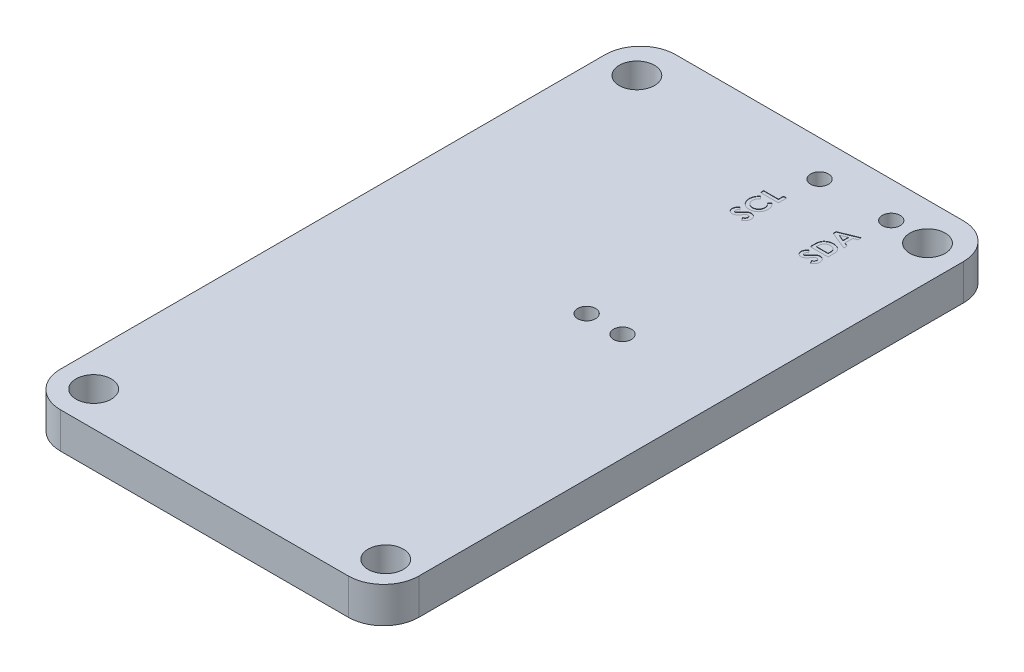
SolidWorks part; units mm, degrees
ref_plane "Front Plane" through (0, 0, 0) normal (0, 0, 1) x (1, 0, 0)
ref_plane "Top Plane" through (0, 0, 0) normal (0, 1, 0) x (1, 0, 0)
ref_plane "Right Plane" through (0, 0, 0) normal (1, 0, 0) x (0, 0, -1)
sketch "Sketch1" plane through (0, 0, 0) normal (0, 1, 0) x (1, 0, 0)
  line L1 (-12.7, -21.8) -> (12.7, -21.8)
  line L2 (-12.7, -21.8) -> (-12.7, 21.8)
  line L3 (-12.7, 21.8) -> (12.7, 21.8)
  line L4 (12.7, -21.8) -> (12.7, 21.8)
  line L5 (-12.7, -21.8) -> (12.7, 21.8) construction
  line L6 (-12.7, 21.8) -> (12.7, -21.8) construction
  point P0 (0, 0)
  dimension "D1" = 43.6
  dimension "D2" = 25.4
extrude "Boss-Extrude1" add sketch "Sketch1" along normal mid plane 2.54
fillet "Fillet1" radius 2.5 4 edges at (-12.7, 0, -21.8) (12.7, 0, -21.8) (-12.7, 0, 21.8) (12.7, 0, 21.8)
sketch "Sketch2" plane through (0, 1.27, 0) normal (0, 1, 0) x (1, 0, 0)
  line L0 (12.7, -19.3) -> (12.7, 19.3) construction
  line L1 (10.2, 21.8) -> (-10.2, 21.8) construction
  line L2 (2.54, 19.26) -> (2.54, 11.64) construction
  line L3 (7.62, 19.26) -> (7.62, 11.64) construction
  circle A0 centre (7.62, 19.26) radius 0.635
  circle A1 centre (2.54, 19.26) radius 0.635
  circle A2 centre (5.08, 2.75) radius 0.635
  circle A3 centre (2.54, 2.75) radius 0.635
  dimension "D6" = 1.27
  dimension "D1" = 5.08
  dimension "D2" = 5.08
  dimension "D3" = 2.54
  dimension "D4" = 2.54
  dimension "D5" = 7.62
  dimension "D7" = 7.62
  dimension "D8" = 19.05
extrude "Cut-Extrude1" cut sketch "Sketch2" against normal through all
sketch "Sketch4" plane through (0, 1.27, 0) normal (0, 1, 0) x (1, 0, 0)
  text T0 "<b>SCL</b>" font "Century Gothic" height 1.27
  text T1 "<b>SDA</b>" font "Century Gothic" height 1.27
extrude "Cut-Extrude2" cut sketch "Sketch4" against normal blind 0.0254
sketch "Sketch5" plane through (0, 1.27, 0) normal (0, 1, 0) x (1, 0, 0)
  line L1 (-12.7, 19.3) -> (-12.7, -19.3) construction
  line L2 (10.2, 21.8) -> (-10.2, 21.8) construction
  line L3 (-10.2, -21.8) -> (10.2, -21.8) construction
  line L4 (12.7, -19.3) -> (12.7, 19.3) construction
  circle A0 centre (-10.3, 19.15) radius 1.905
  circle A1 centre (-10.3, -19.35) radius 1.905
  circle A2 centre (10.5, -19.45) radius 1.905
  circle A3 centre (10.3, 19.15) radius 1.905
  point P0 (-10.3, 19.15)
  point P2 (-10.3, -19.35)
  point P4 (10.5, -19.45)
  point P14 (10.3, 19.15)
  dimension "D1" = 3.81
  dimension "D2" = 2.4
  dimension "D3" = 2.65
  dimension "D4" = 2.45
  dimension "D5" = 2.4
  dimension "D6" = 2.2
  dimension "D7" = 2.65
  dimension "D8" = 2.4
  dimension "D9" = 2.35
hole_wizard "Ø2.5mm Dowel Hole1" positions "Sketch5" profile "Sketch6" hole size "Ø2.5" standard "ANSI Metric" end condition through all
sketch "Sketch6" plane through (-10.3, 1.27, -19.15) normal (1, 0, 0) x (0, 0, 1)
  line L0 (0, 0) -> (0, 2.54)
  line L1 (0, 2.54) -> (1.25, 2.54)
  line L2 (1.25, 2.54) -> (1.25, 0)
  line L5 (1.25, 0) -> (0, 0)
  line L11 (0, -6.35) -> (0, 107.95) construction
  dimension "Thru Hole Dia." = 2.5
  dimension "Thru Hole Depth" = 2.54
